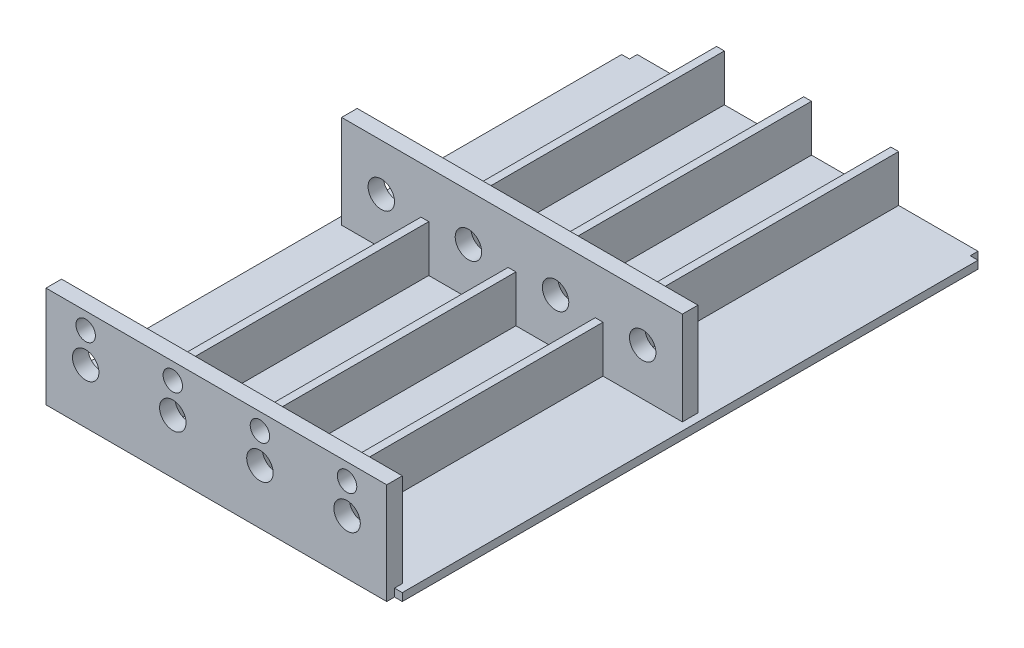
SolidWorks part; units mm, degrees
ref_plane "Front Plane" through (0, 0, 0) normal (0, 0, 1) x (1, 0, 0)
ref_plane "Top Plane" through (0, 0, 0) normal (0, 1, 0) x (1, 0, 0)
ref_plane "Right Plane" through (0, 0, 0) normal (1, 0, 0) x (0, 0, -1)
sketch "Sketch2" plane through (0, 0, 0) normal (0, 0, 1) x (1, 0, 0)
  line L0 (-24.5065, 76.6361) -> (-24.5065, 70.6361)
  line L1 (-24.5065, 76.6361) -> (-25.5065, 76.6361)
  line L2 (-25.5065, 76.6361) -> (-25.5065, 70.6361)
  line L3 (-35.7065, 70.6361) -> (-36.7065, 70.6361)
  line L4 (-36.7065, 70.6361) -> (-36.7065, 69.6361)
  line L5 (8.0935, 70.6361) -> (9.0935, 70.6361)
  line L6 (-24.5065, 70.6361) -> (-14.3065, 70.6361)
  line L7 (-35.7065, 70.6361) -> (-25.5065, 70.6361)
  line L8 (-14.3065, 70.6361) -> (-14.3065, 76.6361)
  line L9 (-14.3065, 76.6361) -> (-13.3065, 76.6361)
  line L10 (-2.1065, 76.6361) -> (-2.1065, 70.6361)
  line L11 (-13.3065, 76.6361) -> (-13.3065, 70.6361)
  line L12 (-13.3065, 70.6361) -> (-3.1065, 70.6361)
  line L13 (-3.1065, 70.6361) -> (-3.1065, 76.6361)
  line L14 (-3.1065, 76.6361) -> (-2.1065, 76.6361)
  line L15 (-2.1065, 70.6361) -> (8.0935, 70.6361)
  line L16 (9.0935, 70.6361) -> (9.0935, 69.6361)
  line L17 (9.0935, 69.6361) -> (-36.7065, 69.6361)
extrude "Gearbox Mount" add sketch "Sketch2" along normal blind 76
sketch "Sketch7" plane through (0, 0, 0) normal (0, 0, 1) x (1, 0, 0)
  line L0 (-24.5065, 70.6361) -> (-24.5065, 82.6361)
  line L1 (-19.4065, 76.6361) -> (-8.2065, 76.6361) construction
  line L2 (-25.5065, 82.6361) -> (-24.5065, 82.6361)
  line L3 (-35.7065, 70.6361) -> (-35.7065, 82.6361)
  line L4 (-35.7065, 82.6361) -> (-25.5065, 82.6361)
  line L5 (-19.4065, 70.6361) -> (-19.4065, 76.6361) construction
  line L6 (-14.3065, 70.6361) -> (-24.5065, 70.6361) construction
  line L7 (-19.4065, 76.6361) -> (-30.6065, 76.6361) construction
  line L8 (-24.5065, 82.6361) -> (-14.3065, 82.6361)
  line L9 (-14.3065, 82.6361) -> (-14.3065, 70.6361)
  line L10 (-14.3065, 70.6361) -> (-24.5065, 70.6361)
  line L11 (-25.5065, 82.6361) -> (-25.5065, 70.6361)
  line L12 (-25.5065, 70.6361) -> (-35.7065, 70.6361)
  line L13 (-13.3065, 70.6361) -> (-13.3065, 82.6361)
  line L14 (-13.3065, 82.6361) -> (-3.1065, 82.6361)
  line L15 (-3.1065, 82.6361) -> (-3.1065, 70.6361)
  line L16 (-3.1065, 70.6361) -> (-13.3065, 70.6361)
  line L17 (-25.5065, 76.6361) -> (-24.5065, 76.6361)
  line L18 (-14.3065, 82.6361) -> (-13.3065, 82.6361)
  line L19 (-13.3065, 76.6361) -> (-14.3065, 76.6361)
  line L20 (-8.2065, 76.6361) -> (2.9935, 76.6361) construction
  line L21 (-2.1065, 70.6361) -> (8.0935, 70.6361)
  line L22 (-2.1065, 70.6361) -> (-2.1065, 82.6361)
  line L23 (-2.1065, 82.6361) -> (8.0935, 82.6361)
  line L24 (8.0935, 70.6361) -> (8.0935, 82.6361)
  line L25 (-3.1065, 82.6361) -> (-2.1065, 82.6361)
  line L26 (-3.1065, 76.6361) -> (-2.1065, 76.6361)
  circle A0 centre (-19.4065, 76.6361) radius 1.7
  circle A1 centre (-30.6065, 76.6361) radius 1.7
  circle A2 centre (-8.2065, 76.6361) radius 1.7
  circle A3 centre (2.9935, 76.6361) radius 1.7
extrude "Boss-Extrude6" add sketch "Sketch7" against normal mid plane 2 from offset 37
sketch "Sketch8" plane through (0, 0, 0) normal (0, 0, 1) x (1, 0, 0)
  line L0 (-30.6065, 76.6361) -> (-19.4065, 76.6361) construction
  line L1 (-19.4065, 76.6361) -> (-8.2065, 76.6361) construction
  line L2 (-35.7065, 70.6361) -> (-35.7065, 82.6361)
  line L3 (-35.7065, 82.6361) -> (-25.5065, 82.6361)
  line L4 (-25.5065, 82.6361) -> (-24.5065, 82.6361)
  line L5 (-24.5065, 76.6361) -> (-25.5065, 76.6361)
  line L6 (-25.5065, 82.6361) -> (-25.5065, 70.6361)
  line L7 (-24.5065, 82.6361) -> (-14.3065, 82.6361)
  line L8 (-25.5065, 70.6361) -> (-35.7065, 70.6361)
  line L9 (-24.5065, 70.6361) -> (-24.5065, 82.6361)
  line L10 (-14.3065, 82.6361) -> (-13.3065, 82.6361)
  line L11 (-14.3065, 82.6361) -> (-14.3065, 70.6361)
  line L12 (-8.2065, 76.6361) -> (2.9935, 76.6361) construction
  line L13 (-14.3065, 70.6361) -> (-24.5065, 70.6361)
  line L14 (-13.3065, 70.6361) -> (-13.3065, 82.6361)
  line L15 (-13.3065, 82.6361) -> (-3.1065, 82.6361)
  line L16 (-3.1065, 82.6361) -> (-3.1065, 70.6361)
  line L17 (-13.3065, 76.6361) -> (-14.3065, 76.6361)
  line L18 (-3.1065, 70.6361) -> (-13.3065, 70.6361)
  line L19 (-2.1065, 70.6361) -> (8.0935, 70.6361)
  line L20 (-2.1065, 70.6361) -> (-2.1065, 82.6361)
  line L21 (-2.1065, 82.6361) -> (8.0935, 82.6361)
  line L22 (8.0935, 70.6361) -> (8.0935, 82.6361)
  line L23 (-3.1065, 82.6361) -> (-2.1065, 82.6361)
  line L24 (-3.1065, 76.6361) -> (-2.1065, 76.6361)
  line L25 (-30.6065, 74.9361) -> (-30.6065, 70.6361) construction
  line L26 (-19.4065, 74.9361) -> (-19.4065, 70.6361) construction
  line L27 (-30.6065, 78.3361) -> (-30.6065, 82.6361) construction
  line L28 (-19.4065, 78.3361) -> (-19.4065, 82.6361) construction
  line L29 (-8.2065, 74.9361) -> (-8.2065, 70.6361) construction
  line L30 (-8.2065, 78.3361) -> (-8.2065, 82.6361) construction
  line L31 (2.9935, 74.9361) -> (2.9935, 70.6361) construction
  line L32 (2.9935, 78.3361) -> (2.9935, 82.6361) construction
  circle A0 centre (-19.4065, 76.6361) radius 1.7
  circle A1 centre (-30.6065, 76.6361) radius 1.7
  circle A2 centre (-8.2065, 76.6361) radius 1.7
  circle A3 centre (2.9935, 76.6361) radius 1.7
  circle A8 centre (-30.6065, 80.4861) radius 1.25
  circle A9 centre (-19.4065, 80.4861) radius 1.25
  circle A10 centre (-8.2065, 80.4861) radius 1.25
  circle A11 centre (2.9935, 80.4861) radius 1.25
extrude "Boss-Extrude7" add sketch "Sketch8" against normal mid plane 2 from offset 75
sketch "Sketch9" plane through (0, 0, 0) normal (0, 1, 0) x (1, 0, 0)
  line L0 (8.0935, -74) -> (8.0935, -76) construction
  line L1 (-36.7065, 0) -> (-35.7065, 0)
  line L2 (-36.7065, 0) -> (-36.7065, -1)
  line L3 (-36.7065, -1) -> (-35.7065, -1)
  line L4 (-35.7065, 0) -> (-35.7065, -1)
  line L5 (9.0935, 0) -> (8.0935, 0)
  line L6 (9.0935, 0) -> (9.0935, -1)
  line L7 (9.0935, -1) -> (8.0935, -1)
  line L8 (8.0935, 0) -> (8.0935, -1)
  line L9 (9.0935, -76) -> (8.0935, -76)
  line L10 (9.0935, -76) -> (9.0935, -75)
  line L11 (9.0935, -75) -> (8.0935, -75)
  line L12 (8.0935, -76) -> (8.0935, -75)
  line L14 (-36.7065, -76) -> (-35.7065, -76)
  line L15 (-36.7065, -76) -> (-36.7065, -75)
  line L16 (-36.7065, -75) -> (-35.7065, -75)
  line L17 (-35.7065, -76) -> (-35.7065, -75)
extrude "Cut-Extrude1" cut sketch "Sketch9" along normal through all
